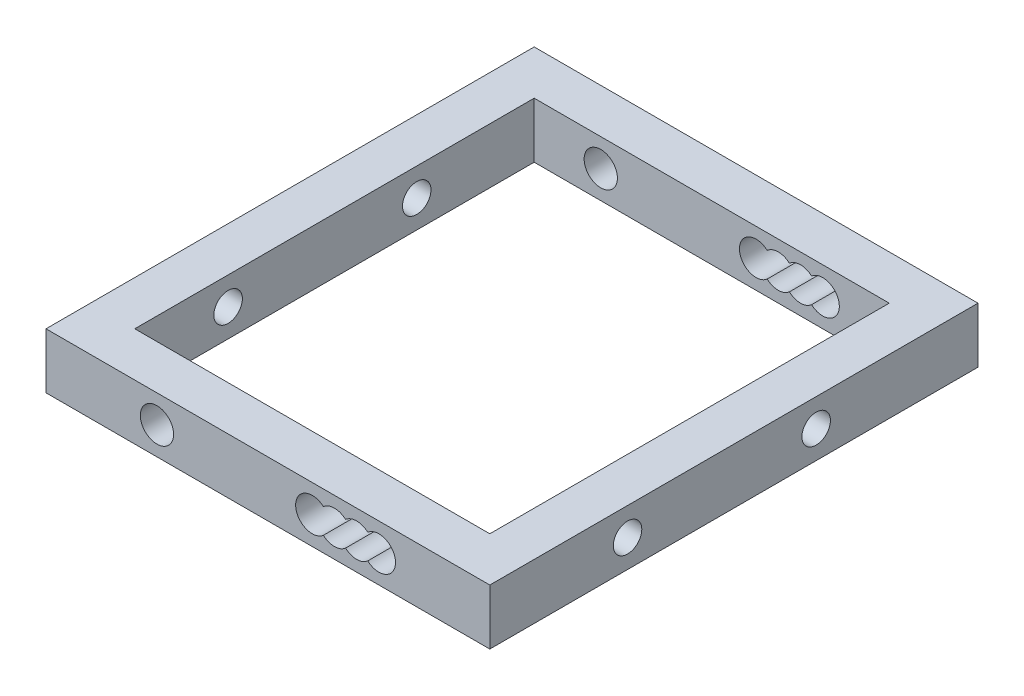
SolidWorks part; units mm, degrees
material "Náilon 6/10"
ref_plane "Plano frontal" through (0, 0, 0) normal (0, 0, 1) x (1, 0, 0)
ref_plane "Plano superior" through (0, 0, 0) normal (0, 1, 0) x (1, 0, 0)
ref_plane "Plano direito" through (0, 0, 0) normal (1, 0, 0) x (0, 0, -1)
sketch "Esboço1" plane through (0, 0, 0) normal (0, 0, 1) x (1, 0, 0)
  line L0 (7.0879, -1.1075) -> (16, -2.5) construction
  line L1 (-16, -2.5) -> (16, -2.5)
  line L2 (-16, -2.5) -> (-16, 2.5)
  line L3 (-16, 2.5) -> (16, 2.5)
  line L4 (16, -2.5) -> (16, 2.5)
  line L5 (-16, -2.5) -> (16, 2.5) construction
  line L6 (-16, 2.5) -> (2.5541, -0.3991) construction
  circle A0 centre (-10, 0) radius 1.5
  arc A1 (5, 1.118) -> (5, -1.118) centre (4, 0) ccw
  arc A2 (7, 1.118) -> (5, 1.118) centre (6, 0) ccw
  arc A3 (7, -1.118) -> (9, -1.118) centre (8, 0) ccw
  arc A4 (5, -1.118) -> (7, -1.118) centre (6, 0) ccw
  arc A5 (9, -1.118) -> (9, 1.118) centre (10, 0) ccw
  arc A6 (9, 1.118) -> (7, 1.118) centre (8, 0) ccw
  point P0 (0, 0)
  dimension "D3" = 3
  dimension "D1" = 32
  dimension "D2" = 5
  dimension "D4" = 6
  dimension "D5" = 14
  dimension "D6" = 16
  dimension "D7" = 18
  dimension "D8" = 20
extrude "Ressalto-extrusão1" add sketch "Esboço1" along normal blind 4
sketch "Esboço3" plane through (0, 0, 4) normal (0, 0, 1) x (1, 0, 0)
  line L1 (16, -2.5) -> (20, -2.5)
  line L2 (16, -2.5) -> (16, 2.5)
  line L3 (16, 2.5) -> (20, 2.5)
  line L4 (20, -2.5) -> (20, 2.5)
  dimension "D1" = 4
extrude "Ressalto-extrusão2" add sketch "Esboço3" against normal blind 44
pattern_linear "Padrão linear1" count 2 spacing 40 along (0, 0, -1) of "Ressalto-extrusão1"
mirror "Espelhar1" about plane through (0, 0, 0) normal (1, 0, 0) of "Ressalto-extrusão2"
sketch "Esboço4" plane through (20, 0, 0) normal (1, 0, 0) x (0, 0, -1)
  line L1 (0, 0) -> (33.8258, 0) construction
  circle A0 centre (8.4129, 0) radius 1.2853
  circle A1 centre (25.4129, 0) radius 1.2853
  point P7 (16.9129, 0)
  dimension "D1" = 17
  dimension "D2" = 8.5
extrude "Corte-extrusão1" cut sketch "Esboço4" against normal blind 39
